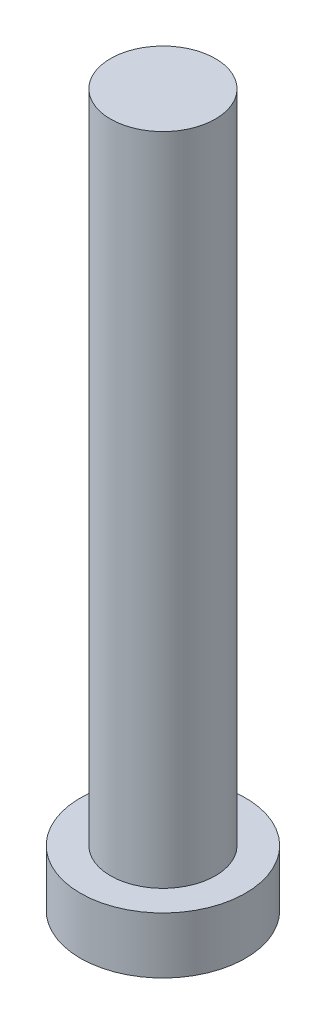
SolidWorks part; units mm, degrees
ref_plane "前视基准面" through (0, 0, 0) normal (0, 0, 1) x (1, 0, 0)
ref_plane "上视基准面" through (0, 0, 0) normal (0, 1, 0) x (1, 0, 0)
ref_plane "右视基准面" through (0, 0, 0) normal (1, 0, 0) x (0, 0, -1)
sketch "草图1" plane through (0, 0, 0) normal (0, 1, 0) x (1, 0, 0)
  circle A0 centre (0, 0) radius 3.15
extrude "凸台-拉伸1" add sketch "草图1" along normal blind 2.15
sketch "草图2" plane through (0, 2.15, 0) normal (0, 1, 0) x (1, 0, 0)
  circle A0 centre (0, 0) radius 2
extrude "凸台-拉伸2" add sketch "草图2" along normal blind 25
sketch "草图3" plane through (0, 0, 0) normal (0, -1, 0) x (1, 0, 0)
  line L0 (-0.5, 1) -> (-0.5, 2)
  line L1 (-2, -0.5) -> (-1, -0.5)
  line L2 (-2, -0.5) -> (-2, 0.5)
  line L3 (-2, 0.5) -> (-1, 0.5)
  line L4 (2, -0.5) -> (2, 0.5)
  line L5 (-2, -0.5) -> (2, 0.5) construction
  line L6 (-2, 0.5) -> (2, -0.5) construction
  line L7 (-0.5, -2) -> (0.5, -2)
  line L8 (-0.5, -2) -> (-0.5, -1)
  line L9 (-0.5, 2) -> (0.5, 2)
  line L10 (0.5, -2) -> (0.5, -1)
  line L11 (-0.5, -2) -> (0.5, 2) construction
  line L12 (-0.5, 2) -> (0.5, -2) construction
  line L13 (1, -0.5) -> (2, -0.5)
  line L14 (0.5, 1) -> (0.5, 2)
  line L15 (1, 0.5) -> (2, 0.5)
  arc A0 (-0.5, -1) -> (-1, -0.5) centre (-1, -1) ccw
  arc A1 (1, -0.5) -> (0.5, -1) centre (1, -1) ccw
  arc A2 (0.5, 1) -> (1, 0.5) centre (1, 1) ccw
  arc A3 (-0.5, 1) -> (-1, 0.5) centre (-1, 1) cw
  point P0 (0, 0)
  point P6 (0, 0)
  point P21 (0.5, 0.5)
  dimension "D1" = 0.5
extrude "切除-拉伸1" cut sketch "草图3" against normal blind 1.5
